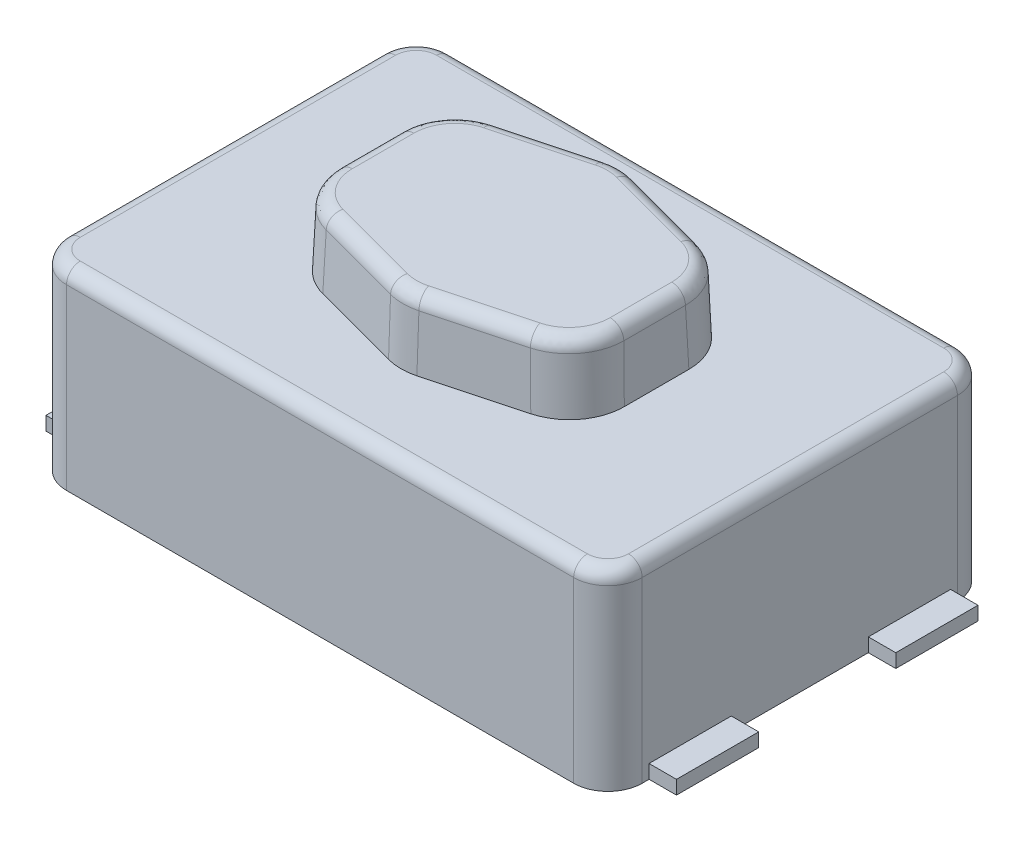
SolidWorks part; units mm, degrees
ref_plane "Front" through (0, 0, 0) normal (0, 0, 1) x (1, 0, 0)
ref_plane "Top" through (0, 0, 0) normal (0, 1, 0) x (1, 0, 0)
ref_plane "Right" through (0, 0, 0) normal (1, 0, 0) x (0, 0, -1)
sketch "Sketch1" plane through (0, 0, 0) normal (0, 1, 0) x (1, 0, 0)
  line L1 (-2.1, 1.4) -> (2.1, 1.4)
  line L2 (-2.1, 1.4) -> (-2.1, -1.4)
  line L3 (-2.1, -1.4) -> (2.1, -1.4)
  line L4 (2.1, 1.4) -> (2.1, -1.4)
  line L5 (-2.1, 1.4) -> (2.1, -1.4) construction
  line L6 (-2.1, -1.4) -> (2.1, 1.4) construction
  point P0 (0, 0)
  dimension "D1" = 4.2
  dimension "D2" = 2.8
extrude "Boss-Extrude1" add sketch "Sketch1" along normal mid plane 1.4
sketch "Sketch2" plane through (0, 0.7, 0) normal (0, 1, 0) x (1, 0, 0)
  line L0 (-1.055, 0.5423) -> (-1.055, -0.5423)
  line L1 (-1.055, -0.5423) -> (0, -0.825)
  line L2 (-1.055, 0) -> (1.055, 0) construction
  line L3 (0, -0.825) -> (1.055, -0.5423)
  line L4 (1.055, -0.5423) -> (1.055, 0.5423)
  line L5 (1.055, 0.5423) -> (0, 0.825)
  line L6 (0, 0.825) -> (0, -0.825) construction
  line L7 (0, 0.825) -> (-1.055, 0.5423)
  dimension "D1" = 15
  dimension "D2" = 2.11
  dimension "D3" = 1.65
extrude "Boss-Extrude2" add sketch "Sketch2" along normal blind 0.5 draft 2 separate body
fillet "Fillet1" radius 0.4 6 edges at (-1.0463, 0.95, -0.5356) (0, 0.95, -0.816) (1.0463, 0.95, -0.5356) (1.0463, 0.95, 0.5356) (0, 0.95, 0.816) (-1.0463, 0.95, 0.5356)
fillet "Fillet2" radius 0.1 12 edges at (0, 1.2, -0.7928) (0.4224, 1.2, -0.6938) (0.9549, 1.2, -0.4655) (1.0375, 1.2, 0) (0.9549, 1.2, 0.4655) (0.4224, 1.2, 0.6938) (0, 1.2, 0.7928) (-0.4224, 1.2, 0.6938) (-0.9549, 1.2, 0.4655) (-1.0375, 1.2, 0) (-0.9549, 1.2, -0.4655) (-0.4224, 1.2, -0.6938)
fillet "Fillet3" radius 0.25 4 edges at (-2.1, 0, 1.4) (-2.1, 0, -1.4) (2.1, 0, -1.4) (2.1, 0, 1.4)
fillet "Fillet4" radius 0.1 8 edges at (-2.0268, 0.7, 1.3268) (-2.1, 0.7, 0) (-2.0268, 0.7, -1.3268) (0, 0.7, -1.4) (2.0268, 0.7, -1.3268) (2.1, 0.7, 0) (2.0268, 0.7, 1.3268) (0, 0.7, 1.4)
sketch "Sketch3" plane through (0, -0.7, 0) normal (0, -1, 0) x (1, 0, 0)
  line L0 (-2.1, -1.15) -> (-2.1, 1.15) construction
  line L1 (-2.1, 0.5) -> (-2.3, 0.5)
  line L2 (-2.1, 0.5) -> (-2.1, 1.1)
  line L3 (-2.1, 1.1) -> (-2.3, 1.1)
  line L4 (-2.3, 0.5) -> (-2.3, 1.1)
  line L5 (0, 1.4) -> (0, -1.4) construction
  line L6 (-1.85, 1.4) -> (1.85, 1.4) construction
  line L7 (1.85, -1.4) -> (-1.85, -1.4) construction
  line L8 (2.1, 0) -> (-2.1, 0) construction
  line L9 (2.1, 1.15) -> (2.1, -1.15) construction
  dimension "D1" = 4.6
  dimension "D2" = 0.6
  dimension "D3" = 2.2
extrude "Boss-Extrude3" add sketch "Sketch3" against normal blind 0.1 contours L4 L3 L2 L1
mirror "Mirror1" about plane through (0, 0, 0) normal (0, 0, 1) of "Boss-Extrude3"
mirror "Mirror2" about plane through (0, 0, 0) normal (1, 0, 0) of "Mirror1", "Boss-Extrude3"
